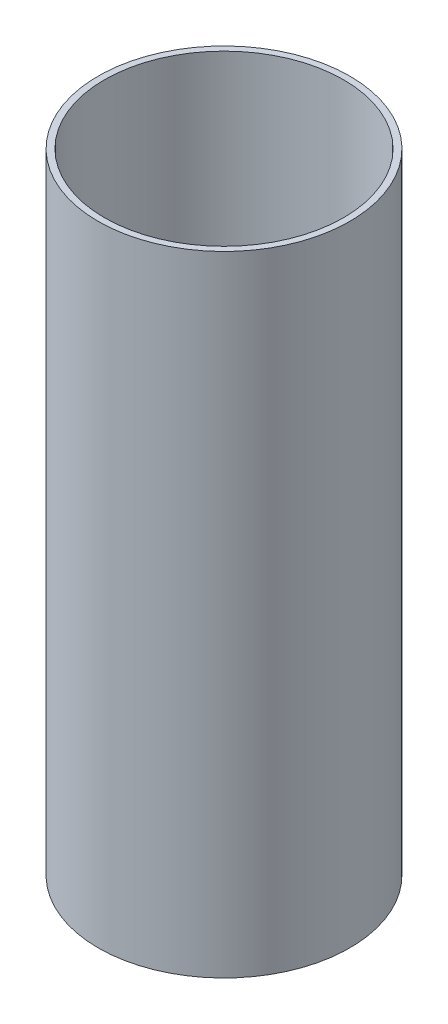
SolidWorks part; units mm, degrees
material "1060 合金"
ref_plane "前视基准面" through (0, 0, 0) normal (0, 0, 1) x (1, 0, 0)
ref_plane "上视基准面" through (0, 0, 0) normal (0, 1, 0) x (1, 0, 0)
ref_plane "右视基准面" through (0, 0, 0) normal (1, 0, 0) x (0, 0, -1)
other "Configuration Table"
sketch "草图1" plane through (0, 0, 0) normal (0, 1, 0) x (1, 0, 0)
  circle A0 centre (0, 0) radius 40
  circle A1 centre (0, 0) radius 38
extrude "凸台-拉伸1" add sketch "草图1" along normal blind 200
